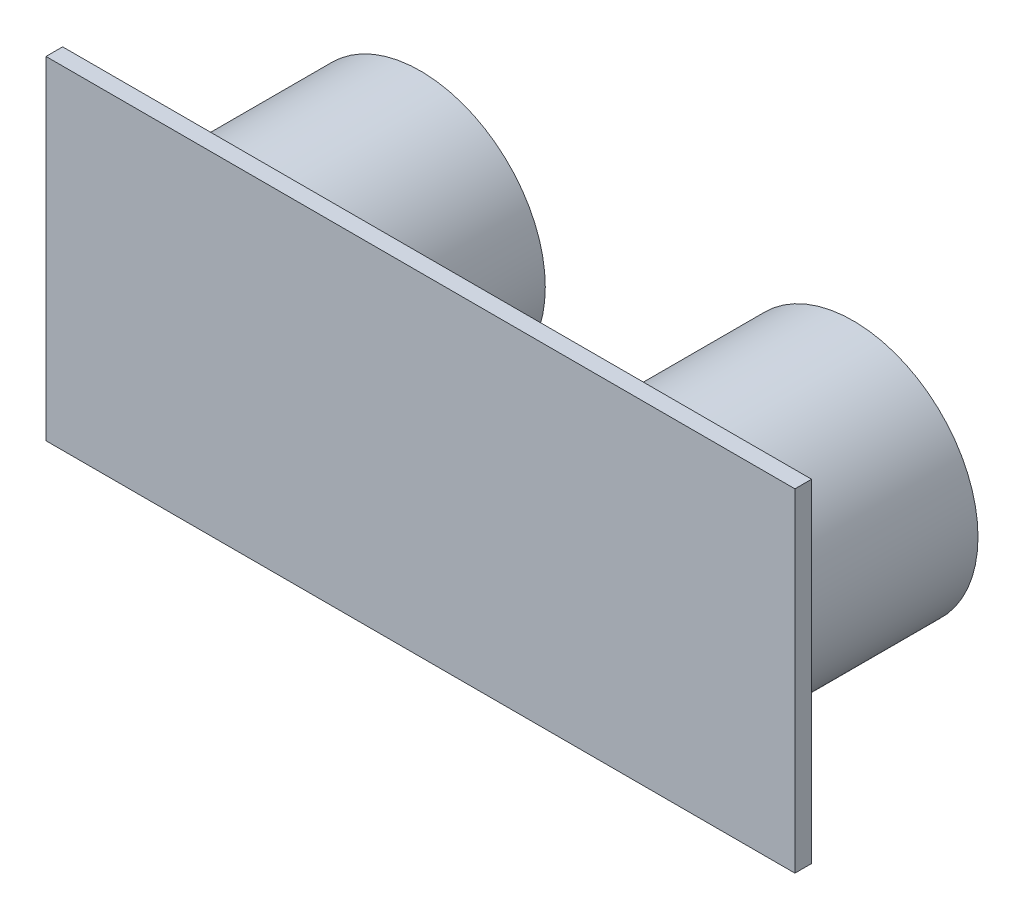
SolidWorks part; units mm, degrees
ref_plane "Front Plane" through (0, 0, 0) normal (0, 0, 1) x (1, 0, 0)
ref_plane "Top Plane" through (0, 0, 0) normal (0, 1, 0) x (1, 0, 0)
ref_plane "Right Plane" through (0, 0, 0) normal (1, 0, 0) x (0, 0, -1)
sketch "Sketch1" plane through (0, 0, 0) normal (0, 0, 1) x (1, 0, 0)
  line L1 (-25.9727, 12.2588) -> (19.0273, 12.2588)
  line L2 (-25.9727, 12.2588) -> (-25.9727, -7.7412)
  line L3 (-25.9727, -7.7412) -> (19.0273, -7.7412)
  line L4 (19.0273, 12.2588) -> (19.0273, -7.7412)
  dimension "D1" = 45
  dimension "D2" = 20
extrude "Boss-Extrude1" add sketch "Sketch1" along normal blind 1
sketch "Sketch2" plane through (0, 0, 0) normal (0, 0, 1) x (1, 0, 0)
  line L0 (-25.9727, 12.2588) -> (-25.9727, -7.7412) construction
  line L1 (19.0273, -7.7412) -> (19.0273, 12.2588) construction
  circle A0 centre (-16.4727, 2.2588) radius 7.5
  circle A1 centre (9.5273, 2.2588) radius 7.5
  circle A2 centre (-16.4727, 2.2588) radius 6.5
  circle A3 centre (9.5273, 2.2588) radius 6.5
  point P8 (19.0273, 2.2588)
  dimension "D3" = 15
  dimension "D4" = 15
  dimension "D5" = 13
  dimension "D6" = 13
  dimension "D1" = 9.5
  dimension "D2" = 9.5
extrude "Boss-Extrude2" add sketch "Sketch2" against normal blind 12
sketch "Sketch3" plane through (0, 0, 0) normal (0, 0, 1) x (1, 0, 0)
  circle A0 centre (9.5273, 2.2588) radius 6.5
  circle A1 centre (-16.4727, 2.2588) radius 6.5
extrude "Boss-Extrude3" add sketch "Sketch3" against normal blind 10
